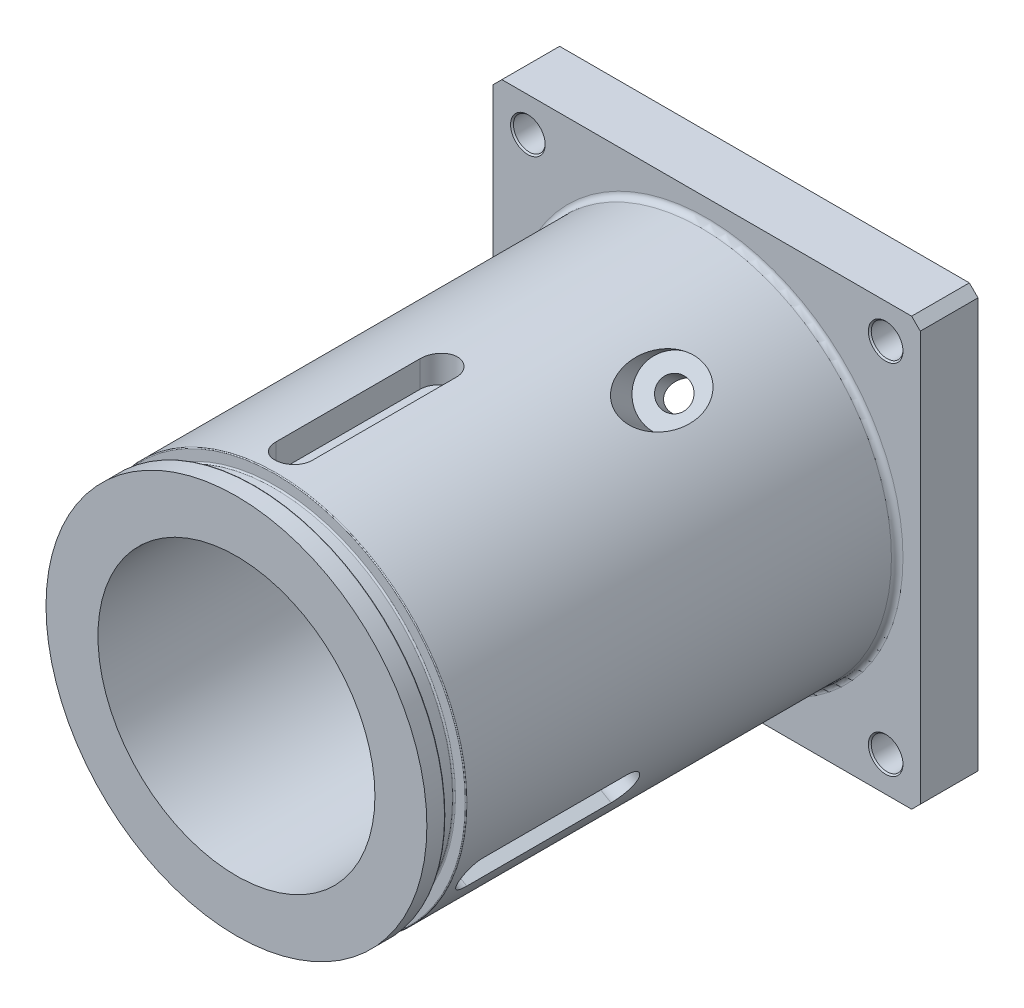
SolidWorks part; units mm, degrees
ref_plane "Plano frontal" through (0, 0, 0) normal (0, 0, 1) x (1, 0, 0)
ref_plane "Plano superior" through (0, 0, 0) normal (0, 1, 0) x (1, 0, 0)
ref_plane "Plano direito" through (0, 0, 0) normal (1, 0, 0) x (0, 0, -1)
sketch "Esboço1" plane through (0, 0, 0) normal (0, 0, 1) x (1, 0, 0)
  line L1 (37, -37) -> (-37, -37)
  line L2 (37, -37) -> (37, 37)
  line L3 (37, 37) -> (-37, 37)
  line L4 (-37, -37) -> (-37, 37)
  line L5 (37, -37) -> (-37, 37) construction
  line L6 (37, 37) -> (-37, -37) construction
  point P0 (0, 0)
  dimension "D1" = 74
  dimension "D2" = 74
extrude "Ressalto-extrusão1" add sketch "Esboço1" along normal blind 10
sketch "Esboço2" plane through (0, 0, 10) normal (0, 0, 1) x (1, 0, 0)
  circle A0 centre (0, 0) radius 33
  circle A1 centre (0, 0) radius 24
  dimension "D1" = 66
  dimension "D2" = 48
extrude "Ressalto-extrusão2" add sketch "Esboço2" along normal blind 81.5
sketch "Esboço3" plane through (0, 0, 10) normal (0, 0, 1) x (1, 0, 0)
  circle A0 centre (0, 0) radius 24
  dimension "D1" = 48
extrude "Corte-extrusão1" cut sketch "Esboço3" against normal through all
sketch "Esboço4" plane through (0, 0, 0) normal (0, 0, -1) x (-1, 0, 0)
  line L5 (31, -31) -> (-31, 31) construction
  line L6 (31, 31) -> (-31, -31) construction
  point P0 (0, 0)
  dimension "D1" = 62
  dimension "D2" = 62
hole_wizard "Furo com folga de M51" positions "Esboço5" profile "Esboço6" hole size "M5" standard "ISO" end condition through all
sketch "Esboço5" plane through (0, 0, 0) normal (0, 0, -1) x (-1, 0, 0)
  point P0 (-31, 31)
  point P3 (-31, -31)
  point P6 (31, -31)
  point P9 (31, 31)
sketch "Esboço6" plane through (31, 31, 0) normal (1, 0, 0) x (0, 1, 0)
  line L0 (0, 0) -> (0, 10)
  line L1 (0, 10) -> (3, 10)
  line L2 (2.75, 9.75) -> (2.75, 0.25)
  line L3 (2.75, 0.25) -> (3, 0)
  line L5 (3, 0) -> (0, 0)
  line L6 (-2.75, 0.25) -> (-3, 0) construction
  line L7 (3, 10) -> (2.75, 9.75)
  line L8 (-3, 10) -> (-2.75, 9.75) construction
  line L11 (0, -6.35) -> (0, 107.95) construction
  dimension "Thru Hole Dia." = 5.5
  dimension "Thru Hole Depth" = 10
  dimension "Near C'Sink Dia." = 6
  dimension "Near C'Sink Angle" = 90
  dimension "Far C'Sink Dia." = 6
  dimension "Far C'Sink Angle" = 90
ref_plane "Plano1" through (-33, 0, 0) normal (-1, 0, 0) x (0, 0, 1)
sketch "Esboço12" plane through (0, 0, 0) normal (1, 0, 0) x (0, 0, -1)
  line L0 (-10, 33) -> (-91.5, 33) construction
  line L1 (-88.3, 33) -> (-84.7, 33)
  line L2 (-88.3, 33) -> (-88.3, 30.9)
  line L3 (-88.3, 30.9) -> (-84.7, 30.9)
  line L4 (-84.7, 33) -> (-84.7, 30.9)
  line L5 (-91.5, 33) -> (-91.5, -33) construction
  line L6 (-91.5, 0) -> (0, 0) construction
  point P6 (-86.5, 33)
  dimension "D1" = 2.1
  dimension "D2" = 3.6
  dimension "D3" = 5
revolve "Corte-Revolução1" cut sketch "Esboço12" angle 360 about L6
fillet "Filete1" radius 0.25 2 edges at (30.9, 0, 84.7) (30.9, 0, 88.3)
fillet "Filete2" radius 0.15 2 edges at (33, 0, 84.7) (33, 0, 88.3)
ref_plane "Plano2" through (33, 0, 0) normal (1, 0, 0) x (0, 0, -1)
sketch "Esboço14" plane through (0, 0, 0) normal (0, 1, 0) x (1, 0, 0)
  line L0 (-33.4904, -34.8492) -> (-18.6412, -20)
  line L1 (-18.6412, -20) -> (-16.8734, -21.7678)
  line L2 (-16.8734, -21.7678) -> (-26.7729, -31.6673)
  line L3 (-26.7729, -31.6673) -> (-24.7557, -33.6845)
  line L4 (-24.7557, -33.6845) -> (-33.4904, -42.4192)
  line L5 (-33.4904, -42.4192) -> (-33.4904, -34.8492)
  line L6 (37, 0) -> (-37, 0) construction
  line L7 (-33, -10) -> (-33, -84.55) construction
  line L8 (-33.4904, -34.8492) -> (20.8655, 19.5067) construction
  dimension "D1" = 2.5
  dimension "D2" = 14
  dimension "D3" = 20
  dimension "D4" = 7.57
  dimension "D5" = 21
  dimension "D6" = 45
  dimension "D7" = 14.3588
revolve "Corte-Revolução2" cut sketch "Esboço14" angle 360 about L8
pattern_circular "PadrãoCircular2" count 3 over 360 about axis through (0, 0, 0) along (0, 0, 1) of "Corte-Revolução2"
chamfer "Chanfro1" distance 1.5 angle 45 4 edges at (37, 37, 5) (-37, 37, 5) (-37, -37, 5) (37, -37, 5)
fillet "Filete3" radius 1 1 edges at (33, 0, 10)
ref_plane "Plano3" through (0, 33, 0) normal (0, 1, 0) x (1, 0, 0)
sketch "Esboço15" plane through (0, 33, 0) normal (0, 1, 0) x (1, 0, 0)
  line L2 (-1.9637, -79.55) -> (-1.9637, -54.55) construction
  line L3 (-5.1137, -79.55) -> (-5.1137, -54.55)
  line L4 (1.1863, -79.55) -> (1.1863, -54.55)
  line L6 (33, -84.55) -> (-33, -84.55) construction
  arc A2 (-5.1137, -79.55) -> (1.1863, -79.55) centre (-1.9637, -79.55) ccw
  arc A3 (1.1863, -54.55) -> (-5.1137, -54.55) centre (-1.9637, -54.55) ccw
  point P0 (8.2014, -47.8866)
  point P10 (-1.9637, -67.05)
  dimension "D3" = 25
  dimension "D4" = 6.3
  dimension "D5" = 5
extrude "Corte-extrusão3" cut sketch "Esboço15" against normal blind 5
pattern_circular "PadrãoCircular3" count 3 every 120 about axis through (0, 0, 0) along (0, 0, 1) of "Corte-extrusão3"
